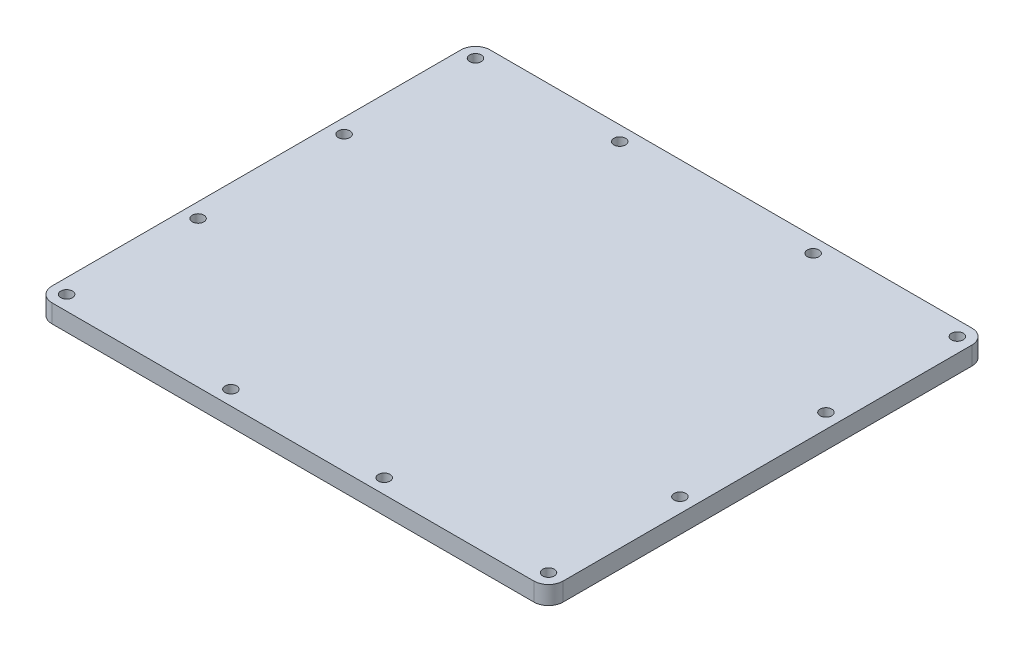
SolidWorks part; units mm, degrees
ref_plane "Front Plane" through (0, 0, 0) normal (0, 0, 1) x (1, 0, 0)
ref_plane "Top Plane" through (0, 0, 0) normal (0, 1, 0) x (1, 0, 0)
ref_plane "Right Plane" through (0, 0, 0) normal (1, 0, 0) x (0, 0, -1)
sketch "Sketch1" plane through (0, 0, 0) normal (0, 1, 0) x (1, 0, 0)
  line L0 (64.5484, 55.3272) -> (70, 60) construction
  line L1 (-66, -60) -> (66, -60)
  line L2 (-70, -56) -> (-70, 56)
  line L3 (-66, 60) -> (66, 60)
  line L4 (70, -56) -> (70, 56)
  line L5 (-70, -60) -> (-64.5484, -55.3272) construction
  line L6 (-70, 60) -> (-5.5749, 4.7785) construction
  line L19 (64.5484, -55.3272) -> (70, -60) construction
  line L20 (-50.7799, -43.5256) -> (-36.8211, -31.5609) construction
  arc A0 (70, -56) -> (66, -60) centre (66, -56) cw
  arc A1 (-70, -56) -> (-66, -60) centre (-66, -56) ccw
  arc A2 (66, 60) -> (70, 56) centre (66, 56) cw
  arc A3 (-66, 60) -> (-70, 56) centre (-66, 56) ccw
  circle A4 centre (-66, 56) radius 1.6
  circle A5 centre (-66, -56) radius 1.6
  circle A6 centre (66, -56) radius 1.6
  circle A7 centre (66, 56) radius 1.6
  circle A8 centre (-66, -20) radius 1.6
  circle A9 centre (66, -20) radius 1.6
  circle A10 centre (-66, 20) radius 1.6
  circle A11 centre (66, 20) radius 1.6
  circle A12 centre (-21, -56) radius 1.6
  circle A13 centre (21, -56) radius 1.6
  circle A14 centre (-26.5, 56) radius 1.6
  circle A15 centre (26.5, 56) radius 1.6
  point P0 (0, 0)
  dimension "D3" = 4
  dimension "D6" = 3.2
  dimension "D9" = 3.2
  dimension "D14" = 3.2
  dimension "D16" = 3.2
  dimension "D20" = 3.2
  dimension "D21" = 3.2
  dimension "D22" = 3.2
  dimension "D25" = 3.2
  dimension "D28" = 3.2
  dimension "D31" = 3.2
  dimension "D34" = 3.2
  dimension "D39" = 3.2
  dimension "D1" = 140
  dimension "D2" = 120
  dimension "D4" = 4
  dimension "D5" = 4
  dimension "D7" = 4
  dimension "D8" = 40
  dimension "D10" = 4
  dimension "D11" = 4
  dimension "D12" = 4
  dimension "D13" = 4
  dimension "D15" = 4
  dimension "D17" = 40
  dimension "D18" = 4
  dimension "D19" = 4
  dimension "D23" = 4
  dimension "D24" = 40
  dimension "D26" = 4
  dimension "D27" = 40
  dimension "D29" = 4
  dimension "D30" = 4
  dimension "D32" = 49
  dimension "D33" = 49
  dimension "D35" = 4
  dimension "D36" = 43.5
  dimension "D37" = 43.5
  dimension "D38" = 4
extrude "Boss-Extrude1" add sketch "Sketch1" along normal blind 5
